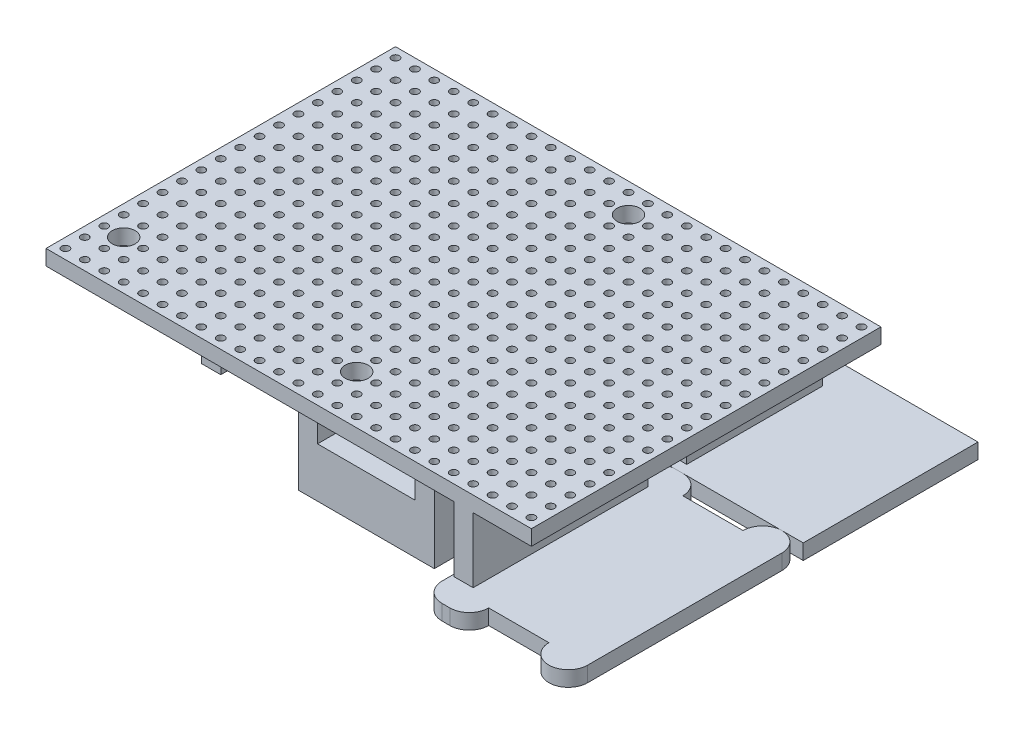
SolidWorks part; units mm, degrees
ref_plane "Front Plane" through (0, 0, 0) normal (0, 0, 1) x (1, 0, 0)
ref_plane "Top Plane" through (0, 0, 0) normal (0, 1, 0) x (1, 0, 0)
ref_plane "Right Plane" through (0, 0, 0) normal (1, 0, 0) x (0, 0, -1)
sketch "Sketch1" plane through (0, 0, 0) normal (0, 1, 0) x (1, 0, 0)
  line L1 (-28.6326, 15.7481) -> (34.8674, 15.7481)
  line L2 (-28.6326, 15.7481) -> (-28.6326, -29.9719)
  line L3 (-28.6326, -29.9719) -> (34.8674, -29.9719)
  line L4 (34.8674, 15.7481) -> (34.8674, -29.9719)
  circle A0 centre (33.5974, -28.7019) radius 0.5
  circle A1 centre (31.0574, -28.7019) radius 0.5
  circle A2 centre (28.5174, -28.7019) radius 0.5
  circle A3 centre (25.9774, -28.7019) radius 0.5
  circle A4 centre (23.4374, -28.7019) radius 0.5
  circle A5 centre (20.8974, -28.7019) radius 0.5
  circle A6 centre (18.3574, -28.7019) radius 0.5
  circle A7 centre (15.8174, -28.7019) radius 0.5
  circle A8 centre (13.2774, -28.7019) radius 0.5
  circle A9 centre (10.7374, -28.7019) radius 0.5
  circle A10 centre (8.1974, -28.7019) radius 0.5
  circle A11 centre (5.6574, -28.7019) radius 0.5
  circle A12 centre (3.1174, -28.7019) radius 0.5
  circle A13 centre (0.5774, -28.7019) radius 0.5
  circle A14 centre (-1.9626, -28.7019) radius 0.5
  circle A15 centre (-4.5026, -28.7019) radius 0.5
  circle A16 centre (-7.0426, -28.7019) radius 0.5
  circle A17 centre (-9.5826, -28.7019) radius 0.5
  circle A18 centre (-12.1226, -28.7019) radius 0.5
  circle A19 centre (-14.6626, -28.7019) radius 0.5
  circle A20 centre (-17.2026, -28.7019) radius 0.5
  circle A21 centre (-19.7426, -28.7019) radius 0.5
  circle A22 centre (-22.2826, -28.7019) radius 0.5
  circle A23 centre (-24.8226, -28.7019) radius 0.5
  circle A24 centre (-27.3626, -28.7019) radius 0.5
  circle A25 centre (31.0574, -26.1619) radius 0.5
  circle A26 centre (28.5174, -26.1619) radius 0.5
  circle A27 centre (25.9774, -26.1619) radius 0.5
  circle A28 centre (23.4374, -26.1619) radius 0.5
  circle A29 centre (20.8974, -26.1619) radius 0.5
  circle A30 centre (18.3574, -26.1619) radius 0.5
  circle A31 centre (15.8174, -26.1619) radius 0.5
  circle A32 centre (13.2774, -26.1619) radius 0.5
  circle A33 centre (10.7374, -26.1619) radius 0.5
  circle A34 centre (8.1974, -26.1619) radius 0.5
  circle A35 centre (5.6574, -26.1619) radius 0.5
  circle A36 centre (3.1174, -26.1619) radius 0.5
  circle A37 centre (0.5774, -26.1619) radius 0.5
  circle A38 centre (-1.9626, -26.1619) radius 0.5
  circle A39 centre (-4.5026, -26.1619) radius 0.5
  circle A40 centre (-7.0426, -26.1619) radius 0.5
  circle A41 centre (-9.5826, -26.1619) radius 0.5
  circle A42 centre (-12.1226, -26.1619) radius 0.5
  circle A43 centre (-14.6626, -26.1619) radius 0.5
  circle A44 centre (-17.2026, -26.1619) radius 0.5
  circle A45 centre (-19.7426, -26.1619) radius 0.5
  circle A46 centre (-22.2826, -26.1619) radius 0.5
  circle A47 centre (-24.8226, -26.1619) radius 0.5
  circle A48 centre (-27.3626, -26.1619) radius 0.5
  circle A49 centre (31.0574, -23.6219) radius 0.5
  circle A50 centre (28.5174, -23.6219) radius 0.5
  circle A51 centre (25.9774, -23.6219) radius 0.5
  circle A52 centre (23.4374, -23.6219) radius 0.5
  circle A53 centre (20.8974, -23.6219) radius 0.5
  circle A54 centre (18.3574, -23.6219) radius 0.5
  circle A55 centre (15.8174, -23.6219) radius 0.5
  circle A56 centre (13.2774, -23.6219) radius 0.5
  circle A57 centre (10.7374, -23.6219) radius 0.5
  circle A58 centre (8.1974, -23.6219) radius 0.5
  circle A59 centre (5.6574, -23.6219) radius 0.5
  circle A60 centre (3.1174, -23.6219) radius 0.5
  circle A61 centre (0.5774, -23.6219) radius 0.5
  circle A62 centre (-1.9626, -23.6219) radius 0.5
  circle A63 centre (-4.5026, -23.6219) radius 0.5
  circle A64 centre (-7.0426, -23.6219) radius 0.5
  circle A65 centre (-9.5826, -23.6219) radius 0.5
  circle A66 centre (-12.1226, -23.6219) radius 0.5
  circle A67 centre (-14.6626, -23.6219) radius 0.5
  circle A68 centre (-17.2026, -23.6219) radius 0.5
  circle A69 centre (-19.7426, -23.6219) radius 0.5
  circle A70 centre (-22.2826, -23.6219) radius 0.5
  circle A71 centre (-24.8226, -23.6219) radius 0.5
  circle A72 centre (-27.3626, -23.6219) radius 0.5
  circle A73 centre (31.0574, -21.0819) radius 0.5
  circle A74 centre (28.5174, -21.0819) radius 0.5
  circle A75 centre (25.9774, -21.0819) radius 0.5
  circle A76 centre (23.4374, -21.0819) radius 0.5
  circle A77 centre (20.8974, -21.0819) radius 0.5
  circle A78 centre (18.3574, -21.0819) radius 0.5
  circle A79 centre (15.8174, -21.0819) radius 0.5
  circle A80 centre (13.2774, -21.0819) radius 0.5
  circle A81 centre (10.7374, -21.0819) radius 0.5
  circle A82 centre (8.1974, -21.0819) radius 0.5
  circle A83 centre (5.6574, -21.0819) radius 0.5
  circle A84 centre (3.1174, -21.0819) radius 0.5
  circle A85 centre (0.5774, -21.0819) radius 0.5
  circle A86 centre (-1.9626, -21.0819) radius 0.5
  circle A87 centre (-4.5026, -21.0819) radius 0.5
  circle A88 centre (-7.0426, -21.0819) radius 0.5
  circle A89 centre (-9.5826, -21.0819) radius 0.5
  circle A90 centre (-12.1226, -21.0819) radius 0.5
  circle A91 centre (-14.6626, -21.0819) radius 0.5
  circle A92 centre (-17.2026, -21.0819) radius 0.5
  circle A93 centre (-19.7426, -21.0819) radius 0.5
  circle A94 centre (-22.2826, -21.0819) radius 0.5
  circle A95 centre (-24.8226, -21.0819) radius 0.5
  circle A96 centre (-27.3626, -21.0819) radius 0.5
  circle A97 centre (31.0574, -18.5419) radius 0.5
  circle A98 centre (28.5174, -18.5419) radius 0.5
  circle A99 centre (25.9774, -18.5419) radius 0.5
  circle A100 centre (23.4374, -18.5419) radius 0.5
  circle A101 centre (20.8974, -18.5419) radius 0.5
  circle A102 centre (18.3574, -18.5419) radius 0.5
  circle A103 centre (15.8174, -18.5419) radius 0.5
  circle A104 centre (13.2774, -18.5419) radius 0.5
  circle A105 centre (10.7374, -18.5419) radius 0.5
  circle A106 centre (8.1974, -18.5419) radius 0.5
  circle A107 centre (5.6574, -18.5419) radius 0.5
  circle A108 centre (3.1174, -18.5419) radius 0.5
  circle A109 centre (0.5774, -18.5419) radius 0.5
  circle A110 centre (-1.9626, -18.5419) radius 0.5
  circle A111 centre (-4.5026, -18.5419) radius 0.5
  circle A112 centre (-7.0426, -18.5419) radius 0.5
  circle A113 centre (-9.5826, -18.5419) radius 0.5
  circle A114 centre (-12.1226, -18.5419) radius 0.5
  circle A115 centre (-14.6626, -18.5419) radius 0.5
  circle A116 centre (-17.2026, -18.5419) radius 0.5
  circle A117 centre (-19.7426, -18.5419) radius 0.5
  circle A118 centre (-22.2826, -18.5419) radius 0.5
  circle A119 centre (-24.8226, -18.5419) radius 0.5
  circle A120 centre (-27.3626, -18.5419) radius 0.5
  circle A121 centre (31.0574, -16.0019) radius 0.5
  circle A122 centre (28.5174, -16.0019) radius 0.5
  circle A123 centre (25.9774, -16.0019) radius 0.5
  circle A124 centre (23.4374, -16.0019) radius 0.5
  circle A125 centre (20.8974, -16.0019) radius 0.5
  circle A126 centre (18.3574, -16.0019) radius 0.5
  circle A127 centre (15.8174, -16.0019) radius 0.5
  circle A128 centre (13.2774, -16.0019) radius 0.5
  circle A129 centre (10.7374, -16.0019) radius 0.5
  circle A130 centre (8.1974, -16.0019) radius 0.5
  circle A131 centre (5.6574, -16.0019) radius 0.5
  circle A132 centre (3.1174, -16.0019) radius 0.5
  circle A133 centre (0.5774, -16.0019) radius 0.5
  circle A134 centre (-1.9626, -16.0019) radius 0.5
  circle A135 centre (-4.5026, -16.0019) radius 0.5
  circle A136 centre (-7.0426, -16.0019) radius 0.5
  circle A137 centre (-9.5826, -16.0019) radius 0.5
  circle A138 centre (-12.1226, -16.0019) radius 0.5
  circle A139 centre (-14.6626, -16.0019) radius 0.5
  circle A140 centre (-17.2026, -16.0019) radius 0.5
  circle A141 centre (-19.7426, -16.0019) radius 0.5
  circle A142 centre (-22.2826, -16.0019) radius 0.5
  circle A143 centre (-24.8226, -16.0019) radius 0.5
  circle A144 centre (-27.3626, -16.0019) radius 0.5
  circle A145 centre (31.0574, -13.4619) radius 0.5
  circle A146 centre (28.5174, -13.4619) radius 0.5
  circle A147 centre (25.9774, -13.4619) radius 0.5
  circle A148 centre (23.4374, -13.4619) radius 0.5
  circle A149 centre (20.8974, -13.4619) radius 0.5
  circle A150 centre (18.3574, -13.4619) radius 0.5
  circle A151 centre (15.8174, -13.4619) radius 0.5
  circle A152 centre (13.2774, -13.4619) radius 0.5
  circle A153 centre (10.7374, -13.4619) radius 0.5
  circle A154 centre (8.1974, -13.4619) radius 0.5
  circle A155 centre (5.6574, -13.4619) radius 0.5
  circle A156 centre (3.1174, -13.4619) radius 0.5
  circle A157 centre (0.5774, -13.4619) radius 0.5
  circle A158 centre (-1.9626, -13.4619) radius 0.5
  circle A159 centre (-4.5026, -13.4619) radius 0.5
  circle A160 centre (-7.0426, -13.4619) radius 0.5
  circle A161 centre (-9.5826, -13.4619) radius 0.5
  circle A162 centre (-12.1226, -13.4619) radius 0.5
  circle A163 centre (-14.6626, -13.4619) radius 0.5
  circle A164 centre (-17.2026, -13.4619) radius 0.5
  circle A165 centre (-19.7426, -13.4619) radius 0.5
  circle A166 centre (-22.2826, -13.4619) radius 0.5
  circle A167 centre (-24.8226, -13.4619) radius 0.5
  circle A168 centre (-27.3626, -13.4619) radius 0.5
  circle A169 centre (31.0574, -10.9219) radius 0.5
  circle A170 centre (28.5174, -10.9219) radius 0.5
  circle A171 centre (25.9774, -10.9219) radius 0.5
  circle A172 centre (23.4374, -10.9219) radius 0.5
  circle A173 centre (20.8974, -10.9219) radius 0.5
  circle A174 centre (18.3574, -10.9219) radius 0.5
  circle A175 centre (15.8174, -10.9219) radius 0.5
  circle A176 centre (13.2774, -10.9219) radius 0.5
  circle A177 centre (10.7374, -10.9219) radius 0.5
  circle A178 centre (8.1974, -10.9219) radius 0.5
  circle A179 centre (5.6574, -10.9219) radius 0.5
  circle A180 centre (3.1174, -10.9219) radius 0.5
  circle A181 centre (0.5774, -10.9219) radius 0.5
  circle A182 centre (-1.9626, -10.9219) radius 0.5
  circle A183 centre (-4.5026, -10.9219) radius 0.5
  circle A184 centre (-7.0426, -10.9219) radius 0.5
  circle A185 centre (-9.5826, -10.9219) radius 0.5
  circle A186 centre (-12.1226, -10.9219) radius 0.5
  circle A187 centre (-14.6626, -10.9219) radius 0.5
  circle A188 centre (-17.2026, -10.9219) radius 0.5
  circle A189 centre (-19.7426, -10.9219) radius 0.5
  circle A190 centre (-22.2826, -10.9219) radius 0.5
  circle A191 centre (-24.8226, -10.9219) radius 0.5
  circle A192 centre (-27.3626, -10.9219) radius 0.5
  circle A193 centre (31.0574, -8.3819) radius 0.5
  circle A194 centre (28.5174, -8.3819) radius 0.5
  circle A195 centre (25.9774, -8.3819) radius 0.5
  circle A196 centre (23.4374, -8.3819) radius 0.5
  circle A197 centre (20.8974, -8.3819) radius 0.5
  circle A198 centre (18.3574, -8.3819) radius 0.5
  circle A199 centre (15.8174, -8.3819) radius 0.5
  circle A200 centre (13.2774, -8.3819) radius 0.5
  circle A201 centre (10.7374, -8.3819) radius 0.5
  circle A202 centre (8.1974, -8.3819) radius 0.5
  circle A203 centre (5.6574, -8.3819) radius 0.5
  circle A204 centre (3.1174, -8.3819) radius 0.5
  circle A205 centre (0.5774, -8.3819) radius 0.5
  circle A206 centre (-1.9626, -8.3819) radius 0.5
  circle A207 centre (-4.5026, -8.3819) radius 0.5
  circle A208 centre (-7.0426, -8.3819) radius 0.5
  circle A209 centre (-9.5826, -8.3819) radius 0.5
  circle A210 centre (-12.1226, -8.3819) radius 0.5
  circle A211 centre (-14.6626, -8.3819) radius 0.5
  circle A212 centre (-17.2026, -8.3819) radius 0.5
  circle A213 centre (-19.7426, -8.3819) radius 0.5
  circle A214 centre (-22.2826, -8.3819) radius 0.5
  circle A215 centre (-24.8226, -8.3819) radius 0.5
  circle A216 centre (-27.3626, -8.3819) radius 0.5
  circle A217 centre (31.0574, -5.8419) radius 0.5
  circle A218 centre (28.5174, -5.8419) radius 0.5
  circle A219 centre (25.9774, -5.8419) radius 0.5
  circle A220 centre (23.4374, -5.8419) radius 0.5
  circle A221 centre (20.8974, -5.8419) radius 0.5
  circle A222 centre (18.3574, -5.8419) radius 0.5
  circle A223 centre (15.8174, -5.8419) radius 0.5
  circle A224 centre (13.2774, -5.8419) radius 0.5
  circle A225 centre (10.7374, -5.8419) radius 0.5
  circle A226 centre (8.1974, -5.8419) radius 0.5
  circle A227 centre (5.6574, -5.8419) radius 0.5
  circle A228 centre (3.1174, -5.8419) radius 0.5
  circle A229 centre (0.5774, -5.8419) radius 0.5
  circle A230 centre (-1.9626, -5.8419) radius 0.5
  circle A231 centre (-4.5026, -5.8419) radius 0.5
  circle A232 centre (-7.0426, -5.8419) radius 0.5
  circle A233 centre (-9.5826, -5.8419) radius 0.5
  circle A234 centre (-12.1226, -5.8419) radius 0.5
  circle A235 centre (-14.6626, -5.8419) radius 0.5
  circle A236 centre (-17.2026, -5.8419) radius 0.5
  circle A237 centre (-19.7426, -5.8419) radius 0.5
  circle A238 centre (-22.2826, -5.8419) radius 0.5
  circle A239 centre (-24.8226, -5.8419) radius 0.5
  circle A240 centre (-27.3626, -5.8419) radius 0.5
  circle A241 centre (31.0574, -3.3019) radius 0.5
  circle A242 centre (28.5174, -3.3019) radius 0.5
  circle A243 centre (25.9774, -3.3019) radius 0.5
  circle A244 centre (23.4374, -3.3019) radius 0.5
  circle A245 centre (20.8974, -3.3019) radius 0.5
  circle A246 centre (18.3574, -3.3019) radius 0.5
  circle A247 centre (15.8174, -3.3019) radius 0.5
  circle A248 centre (13.2774, -3.3019) radius 0.5
  circle A249 centre (10.7374, -3.3019) radius 0.5
  circle A250 centre (8.1974, -3.3019) radius 0.5
  circle A251 centre (5.6574, -3.3019) radius 0.5
  circle A252 centre (3.1174, -3.3019) radius 0.5
  circle A253 centre (0.5774, -3.3019) radius 0.5
  circle A254 centre (-1.9626, -3.3019) radius 0.5
  circle A255 centre (-4.5026, -3.3019) radius 0.5
  circle A256 centre (-7.0426, -3.3019) radius 0.5
  circle A257 centre (-9.5826, -3.3019) radius 0.5
  circle A258 centre (-12.1226, -3.3019) radius 0.5
  circle A259 centre (-14.6626, -3.3019) radius 0.5
  circle A260 centre (-17.2026, -3.3019) radius 0.5
  circle A261 centre (-19.7426, -3.3019) radius 0.5
  circle A262 centre (-22.2826, -3.3019) radius 0.5
  circle A263 centre (-24.8226, -3.3019) radius 0.5
  circle A264 centre (-27.3626, -3.3019) radius 0.5
  circle A265 centre (31.0574, -0.7619) radius 0.5
  circle A266 centre (28.5174, -0.7619) radius 0.5
  circle A267 centre (25.9774, -0.7619) radius 0.5
  circle A268 centre (23.4374, -0.7619) radius 0.5
  circle A269 centre (20.8974, -0.7619) radius 0.5
  circle A270 centre (18.3574, -0.7619) radius 0.5
  circle A271 centre (15.8174, -0.7619) radius 0.5
  circle A272 centre (13.2774, -0.7619) radius 0.5
  circle A273 centre (10.7374, -0.7619) radius 0.5
  circle A274 centre (8.1974, -0.7619) radius 0.5
  circle A275 centre (5.6574, -0.7619) radius 0.5
  circle A276 centre (3.1174, -0.7619) radius 0.5
  circle A277 centre (0.5774, -0.7619) radius 0.5
  circle A278 centre (-1.9626, -0.7619) radius 0.5
  circle A279 centre (-4.5026, -0.7619) radius 0.5
  circle A280 centre (-7.0426, -0.7619) radius 0.5
  circle A281 centre (-9.5826, -0.7619) radius 0.5
  circle A282 centre (-12.1226, -0.7619) radius 0.5
  circle A283 centre (-14.6626, -0.7619) radius 0.5
  circle A284 centre (-17.2026, -0.7619) radius 0.5
  circle A285 centre (-19.7426, -0.7619) radius 0.5
  circle A286 centre (-22.2826, -0.7619) radius 0.5
  circle A287 centre (-24.8226, -0.7619) radius 0.5
  circle A288 centre (-27.3626, -0.7619) radius 0.5
  circle A289 centre (31.0574, 1.7781) radius 0.5
  circle A290 centre (28.5174, 1.7781) radius 0.5
  circle A291 centre (25.9774, 1.7781) radius 0.5
  circle A292 centre (23.4374, 1.7781) radius 0.5
  circle A293 centre (20.8974, 1.7781) radius 0.5
  circle A294 centre (18.3574, 1.7781) radius 0.5
  circle A295 centre (15.8174, 1.7781) radius 0.5
  circle A296 centre (13.2774, 1.7781) radius 0.5
  circle A297 centre (10.7374, 1.7781) radius 0.5
  circle A298 centre (8.1974, 1.7781) radius 0.5
  circle A299 centre (5.6574, 1.7781) radius 0.5
  circle A300 centre (3.1174, 1.7781) radius 0.5
  circle A301 centre (0.5774, 1.7781) radius 0.5
  circle A302 centre (-1.9626, 1.7781) radius 0.5
  circle A303 centre (-4.5026, 1.7781) radius 0.5
  circle A304 centre (-7.0426, 1.7781) radius 0.5
  circle A305 centre (-9.5826, 1.7781) radius 0.5
  circle A306 centre (-12.1226, 1.7781) radius 0.5
  circle A307 centre (-14.6626, 1.7781) radius 0.5
  circle A308 centre (-17.2026, 1.7781) radius 0.5
  circle A309 centre (-19.7426, 1.7781) radius 0.5
  circle A310 centre (-22.2826, 1.7781) radius 0.5
  circle A311 centre (-24.8226, 1.7781) radius 0.5
  circle A312 centre (-27.3626, 1.7781) radius 0.5
  circle A313 centre (31.0574, 4.3181) radius 0.5
  circle A314 centre (28.5174, 4.3181) radius 0.5
  circle A315 centre (25.9774, 4.3181) radius 0.5
  circle A316 centre (23.4374, 4.3181) radius 0.5
  circle A317 centre (20.8974, 4.3181) radius 0.5
  circle A318 centre (18.3574, 4.3181) radius 0.5
  circle A319 centre (15.8174, 4.3181) radius 0.5
  circle A320 centre (13.2774, 4.3181) radius 0.5
  circle A321 centre (10.7374, 4.3181) radius 0.5
  circle A322 centre (8.1974, 4.3181) radius 0.5
  circle A323 centre (5.6574, 4.3181) radius 0.5
  circle A324 centre (3.1174, 4.3181) radius 0.5
  circle A325 centre (0.5774, 4.3181) radius 0.5
  circle A326 centre (-1.9626, 4.3181) radius 0.5
  circle A327 centre (-4.5026, 4.3181) radius 0.5
  circle A328 centre (-7.0426, 4.3181) radius 0.5
  circle A329 centre (-9.5826, 4.3181) radius 0.5
  circle A330 centre (-12.1226, 4.3181) radius 0.5
  circle A331 centre (-14.6626, 4.3181) radius 0.5
  circle A332 centre (-17.2026, 4.3181) radius 0.5
  circle A333 centre (-19.7426, 4.3181) radius 0.5
  circle A334 centre (-22.2826, 4.3181) radius 0.5
  circle A335 centre (-24.8226, 4.3181) radius 0.5
  circle A336 centre (-27.3626, 4.3181) radius 0.5
  circle A337 centre (31.0574, 6.8581) radius 0.5
  circle A338 centre (28.5174, 6.8581) radius 0.5
  circle A339 centre (25.9774, 6.8581) radius 0.5
  circle A340 centre (23.4374, 6.8581) radius 0.5
  circle A341 centre (20.8974, 6.8581) radius 0.5
  circle A342 centre (18.3574, 6.8581) radius 0.5
  circle A343 centre (15.8174, 6.8581) radius 0.5
  circle A344 centre (13.2774, 6.8581) radius 0.5
  circle A345 centre (10.7374, 6.8581) radius 0.5
  circle A346 centre (8.1974, 6.8581) radius 0.5
  circle A347 centre (5.6574, 6.8581) radius 0.5
  circle A348 centre (3.1174, 6.8581) radius 0.5
  circle A349 centre (0.5774, 6.8581) radius 0.5
  circle A350 centre (-1.9626, 6.8581) radius 0.5
  circle A351 centre (-4.5026, 6.8581) radius 0.5
  circle A352 centre (-7.0426, 6.8581) radius 0.5
  circle A353 centre (-9.5826, 6.8581) radius 0.5
  circle A354 centre (-12.1226, 6.8581) radius 0.5
  circle A355 centre (-14.6626, 6.8581) radius 0.5
  circle A356 centre (-17.2026, 6.8581) radius 0.5
  circle A357 centre (-19.7426, 6.8581) radius 0.5
  circle A358 centre (-22.2826, 6.8581) radius 0.5
  circle A359 centre (-24.8226, 6.8581) radius 0.5
  circle A360 centre (-27.3626, 6.8581) radius 0.5
  circle A361 centre (31.0574, 9.3981) radius 0.5
  circle A362 centre (28.5174, 9.3981) radius 0.5
  circle A363 centre (25.9774, 9.3981) radius 0.5
  circle A364 centre (23.4374, 9.3981) radius 0.5
  circle A365 centre (20.8974, 9.3981) radius 0.5
  circle A366 centre (18.3574, 9.3981) radius 0.5
  circle A367 centre (15.8174, 9.3981) radius 0.5
  circle A368 centre (13.2774, 9.3981) radius 0.5
  circle A369 centre (10.7374, 9.3981) radius 0.5
  circle A370 centre (8.1974, 9.3981) radius 0.5
  circle A371 centre (5.6574, 9.3981) radius 0.5
  circle A372 centre (3.1174, 9.3981) radius 0.5
  circle A373 centre (0.5774, 9.3981) radius 0.5
  circle A374 centre (-1.9626, 9.3981) radius 0.5
  circle A375 centre (-4.5026, 9.3981) radius 0.5
  circle A376 centre (-7.0426, 9.3981) radius 0.5
  circle A377 centre (-9.5826, 9.3981) radius 0.5
  circle A378 centre (-12.1226, 9.3981) radius 0.5
  circle A379 centre (-14.6626, 9.3981) radius 0.5
  circle A380 centre (-17.2026, 9.3981) radius 0.5
  circle A381 centre (-19.7426, 9.3981) radius 0.5
  circle A382 centre (-22.2826, 9.3981) radius 0.5
  circle A383 centre (-24.8226, 9.3981) radius 0.5
  circle A384 centre (-27.3626, 9.3981) radius 0.5
  circle A385 centre (31.0574, 11.9381) radius 0.5
  circle A386 centre (28.5174, 11.9381) radius 0.5
  circle A387 centre (25.9774, 11.9381) radius 0.5
  circle A388 centre (23.4374, 11.9381) radius 0.5
  circle A389 centre (20.8974, 11.9381) radius 0.5
  circle A390 centre (18.3574, 11.9381) radius 0.5
  circle A391 centre (15.8174, 11.9381) radius 0.5
  circle A392 centre (13.2774, 11.9381) radius 0.5
  circle A393 centre (10.7374, 11.9381) radius 0.5
  circle A394 centre (8.1974, 11.9381) radius 0.5
  circle A395 centre (5.6574, 11.9381) radius 0.5
  circle A396 centre (3.1174, 11.9381) radius 0.5
  circle A397 centre (0.5774, 11.9381) radius 0.5
  circle A398 centre (-1.9626, 11.9381) radius 0.5
  circle A399 centre (-4.5026, 11.9381) radius 0.5
  circle A400 centre (-7.0426, 11.9381) radius 0.5
  circle A401 centre (-9.5826, 11.9381) radius 0.5
  circle A402 centre (-12.1226, 11.9381) radius 0.5
  circle A403 centre (-14.6626, 11.9381) radius 0.5
  circle A404 centre (-17.2026, 11.9381) radius 0.5
  circle A405 centre (-19.7426, 11.9381) radius 0.5
  circle A406 centre (-22.2826, 11.9381) radius 0.5
  circle A407 centre (-24.8226, 11.9381) radius 0.5
  circle A408 centre (-27.3626, 11.9381) radius 0.5
  circle A409 centre (33.5974, -26.1619) radius 0.5
  circle A410 centre (33.5974, -23.6219) radius 0.5
  circle A411 centre (33.5974, -21.0819) radius 0.5
  circle A412 centre (33.5974, -18.5419) radius 0.5
  circle A413 centre (33.5974, -16.0019) radius 0.5
  circle A414 centre (33.5974, -13.4619) radius 0.5
  circle A415 centre (33.5974, -10.9219) radius 0.5
  circle A416 centre (33.5974, -8.3819) radius 0.5
  circle A417 centre (33.5974, -5.8419) radius 0.5
  circle A418 centre (33.5974, -3.3019) radius 0.5
  circle A419 centre (33.5974, -0.7619) radius 0.5
  circle A420 centre (33.5974, 1.7781) radius 0.5
  circle A421 centre (33.5974, 4.3181) radius 0.5
  circle A422 centre (33.5974, 6.8581) radius 0.5
  circle A423 centre (33.5974, 9.3981) radius 0.5
  circle A424 centre (33.5974, 11.9381) radius 0.5
  circle A425 centre (33.5974, 14.4781) radius 0.5
  circle A426 centre (31.0574, 14.4781) radius 0.5
  circle A427 centre (28.5174, 14.4781) radius 0.5
  circle A428 centre (25.9774, 14.4781) radius 0.5
  circle A429 centre (23.4374, 14.4781) radius 0.5
  circle A430 centre (20.8974, 14.4781) radius 0.5
  circle A431 centre (18.3574, 14.4781) radius 0.5
  circle A432 centre (15.8174, 14.4781) radius 0.5
  circle A433 centre (13.2774, 14.4781) radius 0.5
  circle A434 centre (10.7374, 14.4781) radius 0.5
  circle A435 centre (8.1974, 14.4781) radius 0.5
  circle A436 centre (5.6574, 14.4781) radius 0.5
  circle A437 centre (3.1174, 14.4781) radius 0.5
  circle A438 centre (0.5774, 14.4781) radius 0.5
  circle A439 centre (-1.9626, 14.4781) radius 0.5
  circle A440 centre (-4.5026, 14.4781) radius 0.5
  circle A441 centre (-7.0426, 14.4781) radius 0.5
  circle A442 centre (-9.5826, 14.4781) radius 0.5
  circle A443 centre (-12.1226, 14.4781) radius 0.5
  circle A444 centre (-14.6626, 14.4781) radius 0.5
  circle A445 centre (-17.2026, 14.4781) radius 0.5
  circle A446 centre (-19.7426, 14.4781) radius 0.5
  circle A447 centre (-22.2826, 14.4781) radius 0.5
  circle A448 centre (-24.8226, 14.4781) radius 0.5
  circle A449 centre (-27.3626, 14.4781) radius 0.5
  dimension "D3" = 1
  dimension "D1" = 45.72
  dimension "D2" = 63.5
  dimension "D6" = 1.27
  dimension "D7" = 1.27
  dimension "D4" = 25
  dimension "D5" = 18
extrude "Boss-Extrude1" add sketch "Sketch1" along normal blind 2
sketch "Sketch2" plane through (0, 0, 0) normal (0, -1, 0) x (-1, 0, 0)
  line L0 (-34.8674, 15.7481) -> (28.6326, 15.7481) construction
  line L1 (3.2326, -22.3519) -> (-14.5474, -22.3519)
  line L2 (3.2326, -22.3519) -> (3.2326, 15.7481)
  line L3 (3.2326, 15.7481) -> (-14.5474, 15.7481)
  line L4 (-14.5474, -22.3519) -> (-14.5474, 15.7481)
  line L5 (28.6326, 15.7481) -> (28.6326, -29.9719) construction
  dimension "D1" = 25.4
  dimension "D2" = 17.78
  dimension "D3" = 38.1
extrude "Arduino Nano" add sketch "Sketch2" along normal blind 16.5
sketch "Sketch6" plane through (0, 0, -15.7481) normal (0, 0, -1) x (-1, 0, 0)
  line L0 (-14.5474, -16.5) -> (-14.5474, 0) construction
  line L1 (0.7326, 0) -> (-12.0474, 0)
  line L2 (0.7326, 0) -> (0.7326, -10)
  line L3 (0.7326, -10) -> (-12.0474, -10)
  line L4 (-12.0474, 0) -> (-12.0474, -10)
  line L5 (3.2326, -16.5) -> (3.2326, 0) construction
  line L6 (3.2326, 0) -> (28.6326, 0) construction
  dimension "D1" = 10
  dimension "D2" = 2.5
  dimension "D3" = 2.5
extrude "Cut-Extrude2" cut sketch "Sketch6" against normal through all both and the other way through all
sketch "Sketch3" plane through (0, 0, 0) normal (0, -1, 0) x (-1, 0, 0)
  line L1 (28.6326, 15.7481) -> (18.4726, 15.7481)
  line L2 (28.6326, 15.7481) -> (28.6326, -4.5719)
  line L3 (28.6326, -4.5719) -> (18.4726, -4.5719)
  line L4 (18.4726, 15.7481) -> (18.4726, -4.5719)
  dimension "D1" = 20.32
  dimension "D2" = 10.16
extrude "Relay" add sketch "Sketch3" along normal blind 11
sketch "Sketch4" plane through (0, 0, 0) normal (0, -1, 0) x (-1, 0, 0)
  line L0 (3.2326, 15.7481) -> (18.4726, 15.7481) construction
  line L1 (15.9326, 10.6681) -> (13.3926, 10.6681)
  line L2 (15.9326, 10.6681) -> (15.9326, 15.7481)
  line L3 (15.9326, 15.7481) -> (13.3926, 15.7481)
  line L4 (13.3926, 10.6681) -> (13.3926, 15.7481)
  line L5 (18.4726, 15.7481) -> (18.4726, -4.5719) construction
  line L6 (-34.8674, 15.7481) -> (-14.5474, 15.7481) construction
  line L7 (13.3926, 8.1281) -> (15.9326, 8.1281)
  line L8 (13.3926, 8.1281) -> (13.3926, -2.0319)
  line L9 (13.3926, -2.0319) -> (15.9326, -2.0319)
  line L10 (15.9326, 8.1281) -> (15.9326, -2.0319)
  line L11 (13.3926, -4.5719) -> (15.9326, -4.5719)
  line L12 (13.3926, -4.5719) -> (13.3926, -22.3519)
  line L13 (13.3926, -22.3519) -> (15.9326, -22.3519)
  line L14 (15.9326, -4.5719) -> (15.9326, -22.3519)
  line L15 (-19.6274, 8.1281) -> (-17.0874, 8.1281)
  line L16 (-19.6274, 8.1281) -> (-19.6274, 0.5081)
  line L17 (-19.6274, 0.5081) -> (-17.0874, 0.5081)
  line L18 (-17.0874, 8.1281) -> (-17.0874, 0.5081)
  line L19 (-14.5474, 15.7481) -> (-14.5474, -22.3519) construction
  line L20 (28.6326, -29.9719) -> (-34.8674, -29.9719) construction
  line L21 (-27.2474, 15.7481) -> (-24.7074, 15.7481)
  line L22 (-27.2474, 15.7481) -> (-27.2474, -2.0319)
  line L23 (-27.2474, -2.0319) -> (-24.7074, -2.0319)
  line L24 (-24.7074, 15.7481) -> (-24.7074, -2.0319)
  line L25 (-27.2474, -7.1119) -> (-24.7074, -7.1119)
  line L26 (-27.2474, -7.1119) -> (-27.2474, -29.9719)
  line L27 (-27.2474, -29.9719) -> (-24.7074, -29.9719)
  line L28 (-24.7074, -7.1119) -> (-24.7074, -29.9719)
  point P12 (14.6626, 8.1281)
  dimension "D1" = 2.54
  dimension "D2" = 5.08
  dimension "D3" = 2.54
  dimension "D4" = 10.16
  dimension "D5" = 2.54
  dimension "D6" = 2.54
  dimension "D7" = 17.78
  dimension "D8" = 2.54
  dimension "D9" = 7.62
  dimension "D10" = 2.54
  dimension "D11" = 7.62
  dimension "D12" = 2.54
  dimension "D13" = 17.78
  dimension "D14" = 2.54
  dimension "D15" = 5.08
  dimension "D16" = 22.86
extrude "Female Connectors" add sketch "Sketch4" along normal blind 8.5
sketch "Sketch5" plane through (0, 0, 0) normal (0, -1, 0) x (-1, 0, 0)
  circle A2 centre (24.8226, -23.6219) radius 1.5
  circle A3 centre (-5.6574, 11.9381) radius 1.5
  circle A4 centre (-5.6574, -23.6219) radius 1.5
  dimension "D1" = 3
extrude "Mounting Holes" cut sketch "Sketch5" against normal blind 8.5
sketch "Sketch7" plane through (0, -8.5, 0) normal (0, -1, 0) x (-1, 0, 0)
  line L1 (-23.4374, -3.3019) -> (-43.7574, -3.3019)
  line L2 (-23.4374, -3.3019) -> (-23.4374, 19.5581)
  line L3 (-23.4374, 19.5581) -> (-43.7574, 19.5581)
  line L4 (-43.7574, -3.3019) -> (-43.7574, 19.5581)
  line L5 (-27.2474, 15.7481) -> (-27.2474, -2.0319) construction
  line L7 (-27.2474, -2.0319) -> (-24.7074, -2.0319) construction
  point P5 (0, 0)
  dimension "D1" = 22.86
  dimension "D2" = 20.32
  dimension "D3" = 1.27
  dimension "D4" = 3.81
extrude "LSM303" add sketch "Sketch7" along normal blind 2
sketch "Sketch8" plane through (0, -8.5, 0) normal (0, -1, 0) x (1, 0, 0)
  line L0 (24.7074, 29.9719) -> (24.7074, 7.1119) construction
  line L1 (26.9934, 33.7819) -> (28.0094, 33.7819)
  line L2 (24.4534, 31.2419) -> (24.4534, 5.8419)
  line L3 (26.9934, 3.3019) -> (28.0094, 3.3019)
  line L4 (43.5034, 31.2419) -> (43.5034, 5.8419)
  line L9 (28.0094, 5.8419) -> (28.0094, 31.2419) construction
  line L10 (40.9634, 5.8419) -> (28.0094, 5.8419) construction
  line L11 (38.4234, 5.8419) -> (30.5494, 5.8419)
  line L12 (38.4234, 31.2419) -> (30.5494, 31.2419)
  arc A0 (38.4234, 5.8419) -> (43.5034, 5.8419) centre (40.9634, 5.8419) ccw
  arc A1 (43.5034, 31.2419) -> (38.4234, 31.2419) centre (40.9634, 31.2419) ccw
  arc A2 (30.5494, 31.2419) -> (28.0094, 33.7819) centre (28.0094, 31.2419) ccw
  arc A3 (28.0094, 3.3019) -> (30.5494, 5.8419) centre (28.0094, 5.8419) ccw
  arc A5 (26.9934, 33.7819) -> (24.4534, 31.2419) centre (26.9934, 31.2419) ccw
  arc A6 (26.9934, 3.3019) -> (24.4534, 5.8419) centre (26.9934, 5.8419) cw
  point P3 (42.6768, 18.5419)
  point P15 (0, 0)
  point P17 (0, 0)
  point P19 (0, 0)
  dimension "D4" = 5.08
  dimension "D5" = 5.08
  dimension "D7" = 5.08
  dimension "D8" = 5.08
  dimension "D9" = 2.54
  dimension "D10" = 2.54
  dimension "D1" = 19.05
  dimension "D2" = 0.254
  dimension "D3" = 30.48
  dimension "D6" = 3.556
extrude "Gyro" add sketch "Sketch8" along normal blind 2 separate body
